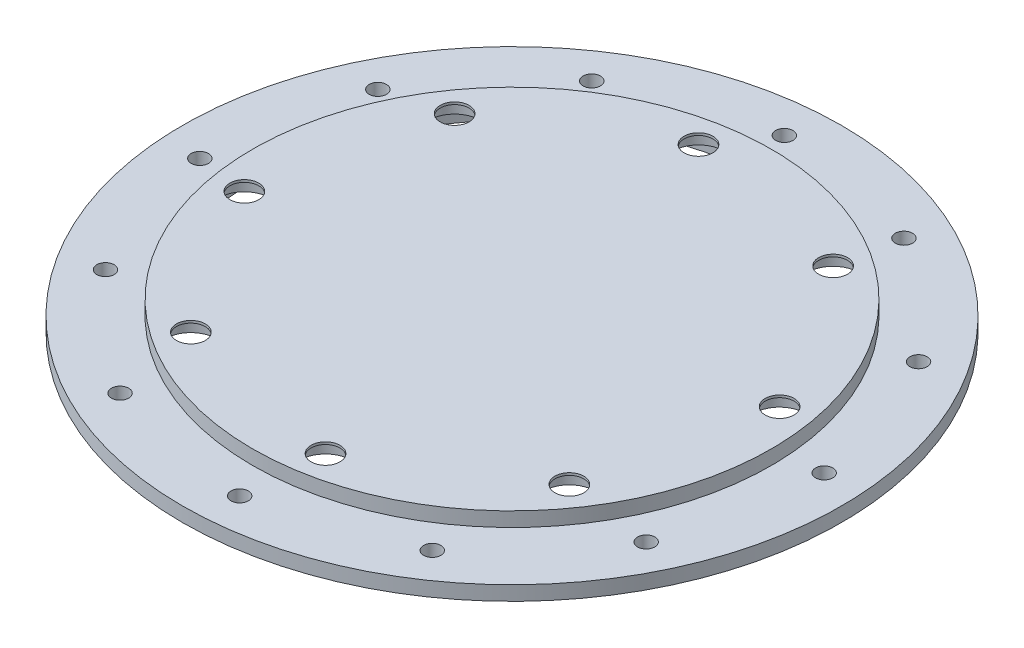
SolidWorks part; units mm, degrees
ref_plane "Front Plane" through (0, 0, 0) normal (0, 0, 1) x (1, 0, 0)
ref_plane "Top Plane" through (0, 0, 0) normal (0, 1, 0) x (1, 0, 0)
ref_plane "Right Plane" through (0, 0, 0) normal (1, 0, 0) x (0, 0, -1)
sketch "Sketch1" plane through (0, 0, 0) normal (0, 1, 0) x (1, 0, 0)
  circle A0 centre (0, 0) radius 114.3
  dimension "D1" = 228.6
extrude "Boss-Extrude1" add sketch "Sketch1" along normal blind 5
sketch "Sketch2" plane through (0, 5, 0) normal (0, 1, 0) x (1, 0, 0)
  circle A0 centre (0, 0) radius 90
  dimension "D1" = 180
extrude "Boss-Extrude2" add sketch "Sketch2" along normal blind 5
sketch "Sketch4" plane through (0, 0, 0) normal (0, -1, 0) x (-1, 0, 0)
  circle A0 centre (0, 0) radius 90
  dimension "D1" = 180
extrude "Cut-Extrude2" cut sketch "Sketch4" against normal blind 3.5
sketch "Sketch5" plane through (0, 10, 0) normal (0, 1, 0) x (1, 0, 0)
  circle A0 centre (0, 0) radius 101.6 construction
  circle A1 centre (0, 0) radius 80 construction
  dimension "D1" = 203.2
  dimension "D2" = 160
hole_wizard "Ø6.0mm Dowel Hole1" positions "Sketch7" profile "Sketch8" hole size "Ø6.0" standard "ANSI Metric" end condition up to next
sketch "Sketch7" plane through (0, 5, 0) normal (0, 1, 0) x (1, 0, 0)
  circle A0 centre (0, 0) radius 101.6 construction
  point P0 (-6.9112, 101.3647)
sketch "Sketch8" plane through (-6.9112, 5, -101.3647) normal (1, 0, 0) x (0, 0, 1)
  line L0 (0, 0) -> (0, 5)
  line L1 (0, 5) -> (3, 5)
  line L2 (3, 5) -> (3, 0)
  line L5 (3, 0) -> (0, 0)
  line L11 (0, -6.35) -> (0, 107.95) construction
  dimension "Thru Hole Dia." = 6
  dimension "Thru Hole Depth" = 5
pattern_circular "CirPattern1" count 12 over 360 about axis through (0, 0, 0) along (0, 1, 0) of "Ø6.0mm Dowel Hole1"
hole_wizard "CBORE for M8 Hex Head Bolt2" positions "Sketch9" profile "Sketch10" counterbore size "M8" standard "ANSI Metric" end condition up to next
sketch "Sketch9" plane through (0, 3.5, 0) normal (0, -1, 0) x (-1, 0, 0)
  circle A0 centre (0, 0) radius 80 construction
  point P0 (-45.7348, 65.6379)
sketch "Sketch10" plane through (45.7348, 3.5, -65.6379) normal (1, 0, 0) x (0, 0, -1)
  line L0 (0, 0) -> (0, 6.5)
  line L1 (0, 6.5) -> (5, 6.5)
  line L3 (5, 6.5) -> (5, 5.68)
  line L4 (5, 5.68) -> (9.005, 5.68)
  line L5 (9.005, 5.68) -> (9.005, 0)
  line L7 (9.005, 0) -> (0, 0)
  line L11 (0, -6.35) -> (0, 107.95) construction
  dimension "Thru Hole Dia." = 10
  dimension "Thru Hole Depth" = 6.5
  dimension "C'Bore Dia." = 18.01
  dimension "C'Bore Depth" = 5.68
pattern_circular "CirPattern2" count 8 over 360 about axis through (0, 0, 0) along (0, 1, 0) of "CBORE for M8 Hex Head Bolt2"
